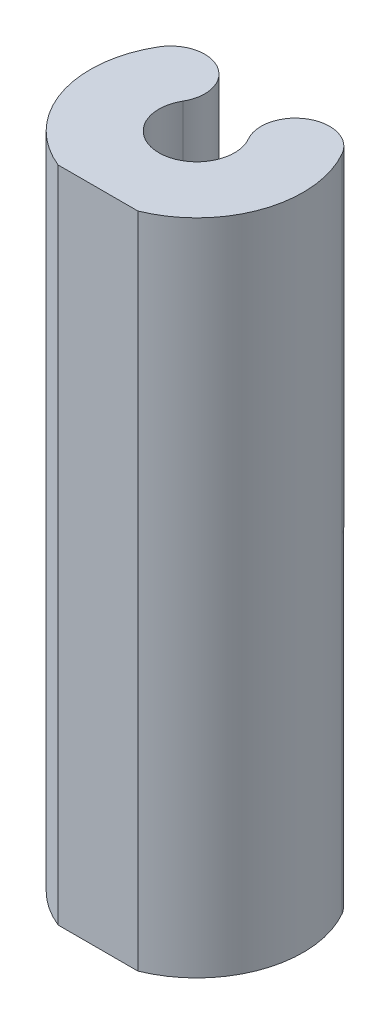
SolidWorks part; units mm, degrees
ref_plane "Front Plane" through (0, 0, 0) normal (0, 0, 1) x (1, 0, 0)
ref_plane "Top Plane" through (0, 0, 0) normal (0, 1, 0) x (1, 0, 0)
ref_plane "Right Plane" through (0, 0, 0) normal (1, 0, 0) x (0, 0, -1)
sketch "Sketch1" plane through (0, 0, 0) normal (0, 1, 0) x (1, 0, 0)
  line L0 (0, 0) -> (0, 4.4069) construction
  circle A0 centre (0, 0) radius 4.4069
  circle A1 centre (0, 0) radius 8.2169
  arc A2 (-3.8128, 2.2098) -> (-7.1092, 4.1203) centre (-5.461, 3.1651) ccw
  arc A3 (3.8128, 2.2098) -> (7.1092, 4.1203) centre (5.461, 3.1651) cw
  point P8 (-3.556, 3.1651)
  point P12 (3.556, 3.1651)
  point P13 (-3.533, 3.2044)
  dimension "D1" = 8.8138
  dimension "D2" = 3.81
  dimension "D3" = 7.112
extrude "Boss-Extrude1" add sketch "Sketch1" along normal blind 25.4 contours A3 A0 A2 A1
sketch "Sketch2" plane through (0, 25.4, 0) normal (0, 1, 0) x (1, 0, 0)
  line L0 (0, -9.0386) -> (0, 9.0386) construction
  circle A0 centre (0, 0) radius 2.921
  arc A1 (-2.5272, 1.4647) -> (-7.1092, 4.1203) centre (-4.8182, 2.7925) ccw
  arc A2 (2.5272, 1.4647) -> (7.1092, 4.1203) centre (4.8182, 2.7925) cw
  arc A4 (7.1092, 4.1203) -> (3.8128, 2.2098) centre (5.461, 3.1651) ccw
  arc A5 (-3.8128, 2.2098) -> (3.8128, 2.2098) centre (0, 0) ccw
  arc A6 (-3.8128, 2.2098) -> (-7.1092, 4.1203) centre (-5.461, 3.1651) ccw
  arc A7 (-7.1092, 4.1203) -> (7.1092, 4.1203) centre (0, 0) ccw
  arc A11 (-7.1092, 4.1203) -> (7.1092, 4.1203) centre (0, 0) ccw
  arc M7 (7.1092, 4.1203) -> (3.8128, 2.2098) centre (5.461, 3.1651) ccw
  arc M8 (3.8128, 2.2098) -> (-3.8128, 2.2098) centre (0, 0) cw
  arc M9 (-3.8128, 2.2098) -> (-7.1092, 4.1203) centre (-5.461, 3.1651) ccw
  arc M10 (-7.1092, 4.1203) -> (7.1092, 4.1203) centre (0, 0) ccw
  dimension "D2" = 5.842
  dimension "D1" = 0
extrude "Boss-Extrude2" add sketch "Sketch2" along normal blind 25.4 contours M10 M7 M8 M9 | A2 A0 A1 M9 M8 M7
sketch "Sketch3" plane through (0, 50.8, 0) normal (0, 1, 0) x (1, 0, 0)
  line L0 (-3.0746, -7.62) -> (3.0746, -7.62)
  arc A0 (-7.1092, 4.1203) -> (7.1092, 4.1203) centre (0, 0) ccw construction
  arc A5 (-7.1092, 4.1203) -> (7.1092, 4.1203) centre (0, 0) ccw
  arc A6 (7.1092, 4.1203) -> (2.5272, 1.4647) centre (4.8182, 2.7925) ccw
  arc A7 (-2.5272, 1.4647) -> (2.5272, 1.4647) centre (0, 0) ccw
  arc A8 (-2.5272, 1.4647) -> (-7.1092, 4.1203) centre (-4.8182, 2.7925) ccw
  arc A9 (-7.1092, 4.1203) -> (7.1092, 4.1203) centre (0, 0) ccw
  arc A10 (7.1092, 4.1203) -> (2.5272, 1.4647) centre (4.8182, 2.7925) ccw
  arc A11 (-2.5272, 1.4647) -> (2.5272, 1.4647) centre (0, 0) ccw
  arc A12 (-2.5272, 1.4647) -> (-7.1092, 4.1203) centre (-4.8182, 2.7925) ccw
  arc M6 (-7.1092, 4.1203) -> (7.1092, 4.1203) centre (0, 0) ccw
  dimension "D1" = 7.62
  dimension "D2" = 0
extrude "Cut-Extrude1" cut sketch "Sketch3" against normal through all contours L0 M6
